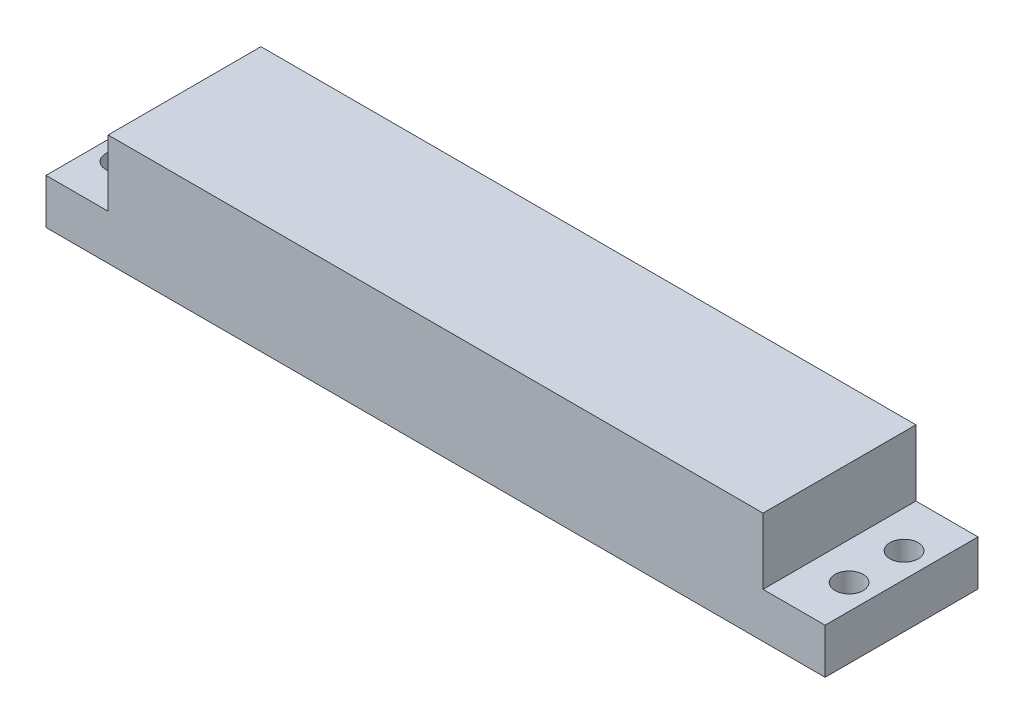
SolidWorks part; units mm, degrees
ref_plane "Front Plane" through (0, 0, 0) normal (0, 0, 1) x (1, 0, 0)
ref_plane "Top Plane" through (0, 0, 0) normal (0, 1, 0) x (1, 0, 0)
ref_plane "Right Plane" through (0, 0, 0) normal (1, 0, 0) x (0, 0, -1)
sketch "Sketch1" plane through (0, 0, 0) normal (0, 1, 0) x (1, 0, 0)
  line L0 (-52.455, 3.955) -> (-52.455, -3.955) construction
  line L1 (-56.05, -11) -> (56.05, -11)
  line L2 (-56.05, -11) -> (-56.05, 11)
  line L3 (-56.05, 11) -> (56.05, 11)
  line L4 (56.05, -11) -> (56.05, 11)
  line L5 (-56.05, -11) -> (56.05, 11) construction
  line L6 (-56.05, 11) -> (56.05, -11) construction
  line L7 (-52.455, 0) -> (52.455, 0) construction
  line L8 (52.455, 3.955) -> (52.455, -3.955) construction
  circle A0 centre (-52.455, 3.955) radius 2.025
  circle A1 centre (-52.455, -3.955) radius 2.025
  circle A2 centre (52.455, -3.955) radius 2.025
  circle A3 centre (52.455, 3.955) radius 2.025
  point P0 (0, 0)
  dimension "D5" = 4.05
  dimension "D1" = 7.91
  dimension "D2" = 22
  dimension "D3" = 112.1
  dimension "D4" = 104.91
extrude "Boss-Extrude1" add sketch "Sketch1" along normal blind 6.5
sketch "Sketch2" plane through (0, 6.5, 0) normal (0, 1, 0) x (1, 0, 0)
  line L0 (56.05, 11) -> (-56.05, 11) construction
  line L1 (47.1199, -11) -> (-47.1199, -11)
  line L2 (47.1199, -11) -> (47.1199, 11)
  line L3 (47.1199, 11) -> (-47.1199, 11)
  line L4 (-47.1199, -11) -> (-47.1199, 11)
  line L5 (47.1199, -11) -> (-47.1199, 11) construction
  line L6 (47.1199, 11) -> (-47.1199, -11) construction
  point P0 (0, 0)
extrude "Boss-Extrude3" add sketch "Sketch2" along normal offset from surface (9.5 mm away) 16 up to face at (-52.455, 0, -1.93)
